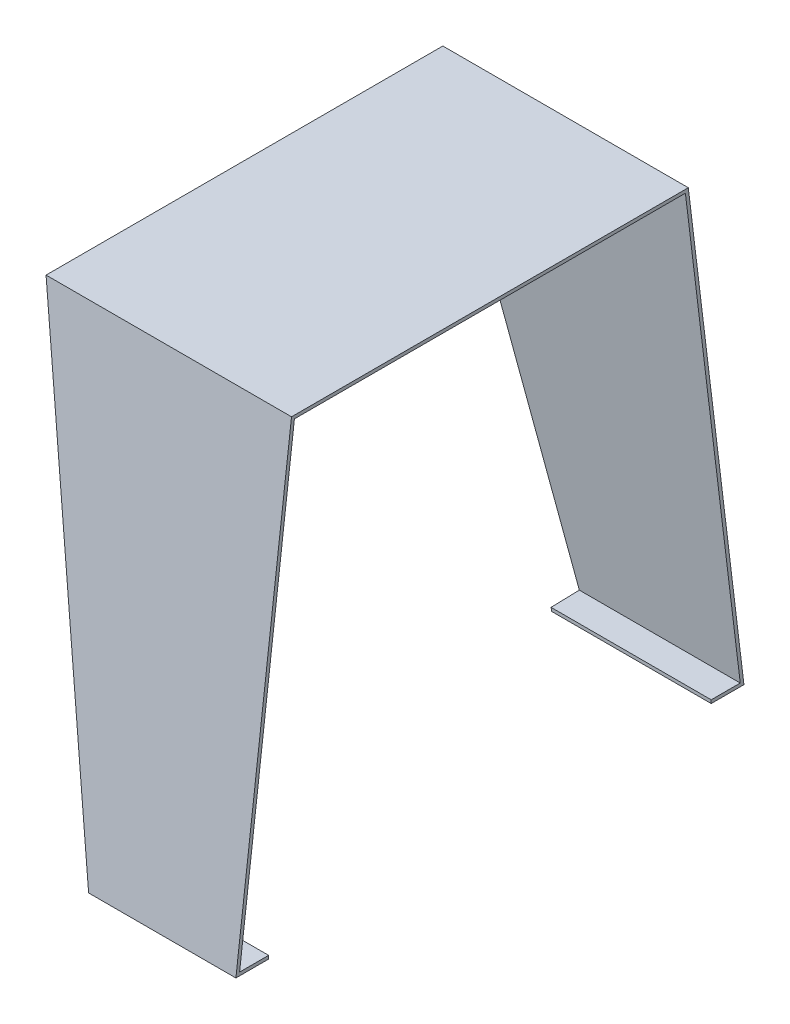
SolidWorks part; units mm, degrees
ref_plane "Front" through (0, 0, 0) normal (0, 0, 1) x (1, 0, 0)
ref_plane "Top" through (0, 0, 0) normal (0, 1, 0) x (1, 0, 0)
ref_plane "Right" through (0, 0, 0) normal (1, 0, 0) x (0, 0, -1)
sketch "草图1" plane through (0, 0, 0) normal (1, 0, 0) x (0, 0, -1)
  line L0 (0, 0) -> (-34, -280)
  line L1 (-34, -280) -> (276.46, -280)
  line L2 (276.46, -280) -> (242.46, 0)
  line L3 (242.46, 0) -> (0, 0)
  line L4 (240.6882, -2) -> (1.7718, -2)
  line L5 (1.7718, -2) -> (-31.7425, -278)
  line L6 (-31.7425, -278) -> (274.2025, -278)
  line L7 (274.2025, -278) -> (240.6882, -2)
  point P5 (121.23, 0)
  point P6 (121.23, -280)
  dimension "D1" = 310.46
  dimension "D2" = 280
  dimension "D3" = 34
  dimension "D4" = 2
extrude "凸台-拉伸1" add sketch "草图1" along normal blind 150
sketch "草图2" plane through (0, 0, 0) normal (0, 0.1205, 0.9927) x (1, 0, 0)
  line L0 (0, 0) -> (0, -282.0567)
  line L2 (0, -282.0567) -> (60, -282.0567)
  line L3 (150, -282.0567) -> (0, -282.0567) construction
  line L4 (60, -282.0567) -> (0, 0)
  dimension "D1" = 60
extrude "切除-拉伸1" cut sketch "草图2" against normal through all
sketch "草图3" plane through (0, -278, 0) normal (0, 1, 0) x (1, 0, 0)
  line L0 (0, 242.46) -> (0, 0) construction
  line L1 (0, 256.46) -> (150, 256.46)
  line L2 (0, 256.46) -> (0, -14)
  line L3 (0, -14) -> (150, -14)
  line L4 (150, 256.46) -> (150, -14)
  line L5 (150, 242.46) -> (150, 0) construction
  line L8 (150, 276.46) -> (52.0391, 276.46) construction
  line L9 (150, -34) -> (60, -34) construction
  dimension "D1" = 20
  dimension "D2" = 20
extrude "切除-拉伸3" cut sketch "草图3" against normal up to next
